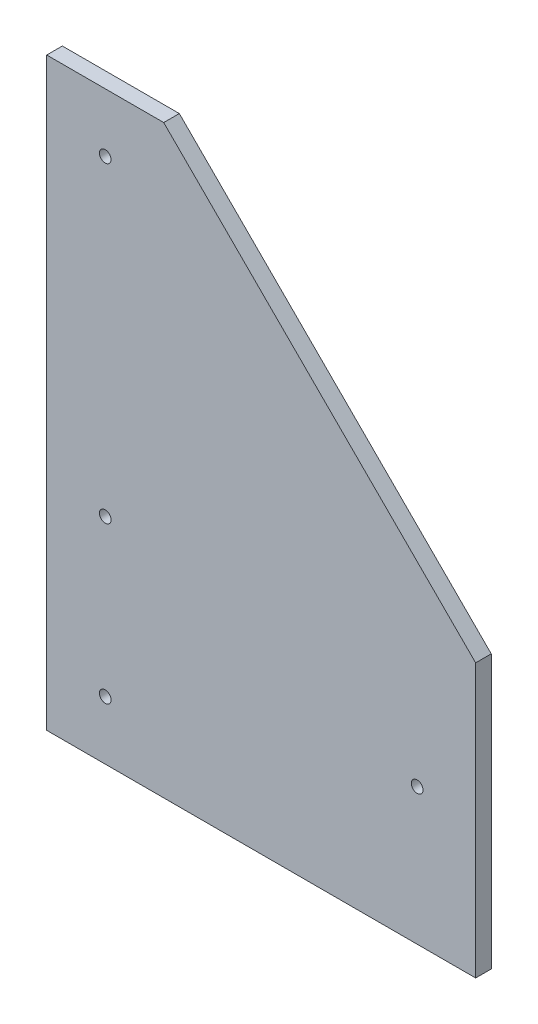
SolidWorks part; units mm, degrees
ref_plane "Front Plane" through (0, 0, 0) normal (0, 0, 1) x (1, 0, 0)
ref_plane "Top Plane" through (0, 0, 0) normal (0, 1, 0) x (1, 0, 0)
ref_plane "Right Plane" through (0, 0, 0) normal (1, 0, 0) x (0, 0, -1)
sketch "Sketch1" plane through (0, 0, 0) normal (0, 0, 1) x (1, 0, 0)
  line L0 (0, 0) -> (139.7, 0)
  line L1 (139.7, 0) -> (139.7, 88.9)
  line L2 (139.7, 88.9) -> (38.1, 190.5)
  line L3 (38.1, 190.5) -> (0, 190.5)
  line L4 (0, 190.5) -> (0, 0)
  dimension "D1" = 88.9
  dimension "D2" = 38.1
  dimension "D3" = 101.6
  dimension "D4" = 101.6
extrude "Boss-Extrude1" add sketch "Sketch1" along normal blind 5.08
hole_wizard "#6 Clearance Hole1" positions "Sketch2" profile "Sketch3" hole size "#6" standard "ANSI Inch" end condition through all
sketch "Sketch2" plane through (0, 0, 5.08) normal (0, 0, 1) x (1, 0, 0)
  line L0 (19.05, 190.5) -> (19.05, 0)
  line L1 (38.1, 190.5) -> (0, 190.5) construction
  line L2 (0, 0) -> (139.7, 0) construction
  line L3 (139.7, 0) -> (139.7, 88.9) construction
  line L4 (19.05, 19.05) -> (120.65, 44.45)
  line L5 (120.65, 44.45) -> (19.05, 69.85)
  point P9 (19.05, 171.45)
  point P11 (19.05, 19.05)
  point P13 (19.05, 69.85)
  point P15 (120.65, 44.45)
  point P20 (139.7, 44.45)
  point P26 (114.1807, 44.45)
  point P27 (19.05, 72.7664)
  dimension "D1" = 19.05
  dimension "D2" = 19.05
  dimension "D3" = 19.05
sketch "Sketch3" plane through (120.65, 44.45, 5.08) normal (1, 0, 0) x (0, -1, 0)
  line L0 (0, 0) -> (0, 5.08)
  line L1 (0, 5.08) -> (1.8986, 5.08)
  line L2 (1.8986, 5.08) -> (1.8986, 0)
  line L5 (1.8986, 0) -> (0, 0)
  line L11 (0, -6.35) -> (0, 107.95) construction
  dimension "Thru Hole Dia." = 3.7973
  dimension "Thru Hole Depth" = 5.08
